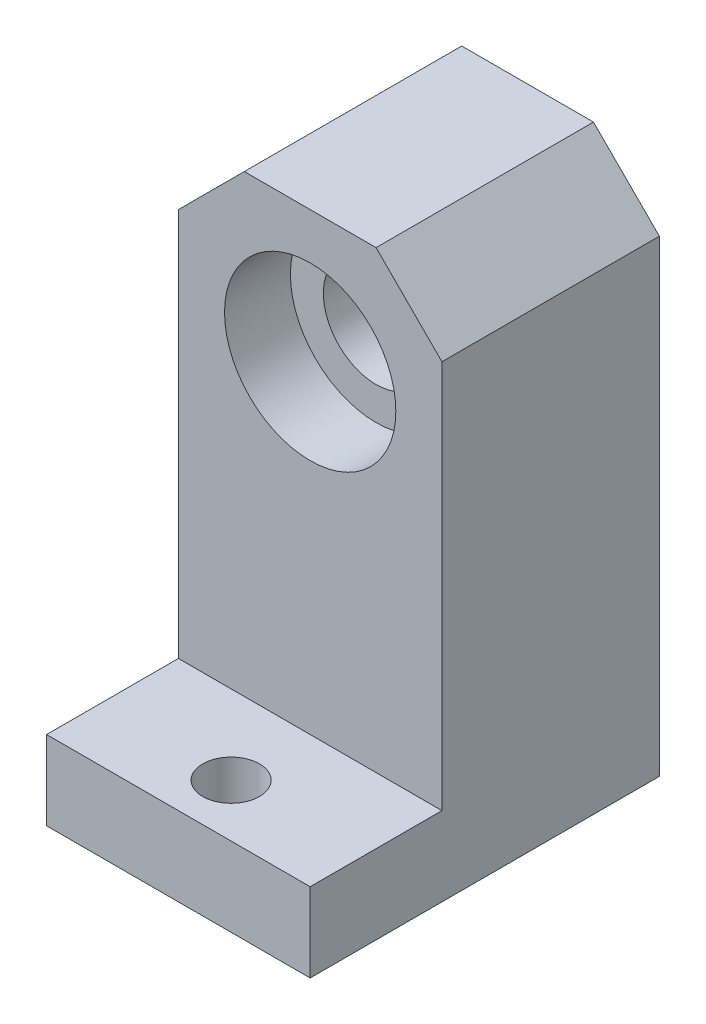
SolidWorks part; units mm, degrees
ref_plane "前视基准面" through (0, 0, 0) normal (0, 0, 1) x (1, 0, 0)
ref_plane "上视基准面" through (0, 0, 0) normal (0, 1, 0) x (1, 0, 0)
ref_plane "右视基准面" through (0, 0, 0) normal (1, 0, 0) x (0, 0, -1)
sketch "草图1" plane through (0, 0, 0) normal (0, 0, 1) x (1, 0, 0)
  line L3 (-10, 0) -> (-10, 40.5)
  line L4 (-10, 40.5) -> (10, 40.5)
  line L5 (0, 40.5) -> (0, 0) construction
  line L6 (10, 0) -> (10, 40.5)
  line L9 (-10, 0) -> (10, 0)
  dimension "D1" = 20
extrude "凸台-拉伸1" add sketch "草图1" along normal mid plane 16.5
sketch "草图2" plane through (0, 0, 8.25) normal (0, 0, 1) x (1, 0, 0)
  line L1 (0, 40.5) -> (0, 0) construction
  line L2 (10, 40.5) -> (-10, 40.5) construction
  line L3 (0, 0) -> (5.1437, -6.2681) construction
  circle A0 centre (0, 30.5) radius 4
  dimension "D1" = 8
  dimension "D3" = 10
extrude "切除-拉伸1" cut sketch "草图2" against normal through all contours A0
sketch "草图3" plane through (0, 0, 8.25) normal (0, 0, 1) x (1, 0, 0)
  circle A0 centre (0, 30.5) radius 6.5
  dimension "D1" = 13
extrude "切除-拉伸2" cut sketch "草图3" against normal blind 5
mirror "镜向1" about plane through (0, 0, 0) normal (0, 0, 1) of "切除-拉伸2"
chamfer "倒角1" distance 5 angle 45 2 edges at (10, 40.5, 0) (-10, 40.5, 0)
sketch "草图4" plane through (10, 0, 0) normal (1, 0, 0) x (0, 0, -1)
  line L0 (-8.25, 0) -> (-18.25, 0)
  line L1 (-18.25, 0) -> (-18.25, 6)
  line L2 (-18.25, 6) -> (-8.25, 6)
  line L3 (-8.25, 0) -> (-8.25, 35.5) construction
  line L4 (-8.25, 6) -> (-8.25, 0)
extrude "凸台-拉伸2" add sketch "草图4" against normal blind 20
sketch "草图5" plane through (0, 6, 0) normal (0, 1, 0) x (1, 0, 0)
  line L0 (-10, -8.25) -> (-10, -18.25) construction
  line L2 (-10, -18.25) -> (10, -18.25) construction
  circle A0 centre (0, -14.25) radius 2.15
  point P0 (0, -14.25)
  point P4 (0, -14.25)
  dimension "D1" = 10
  dimension "D2" = 4
extrude "切除-拉伸3" cut sketch "草图5" against normal blind 17
